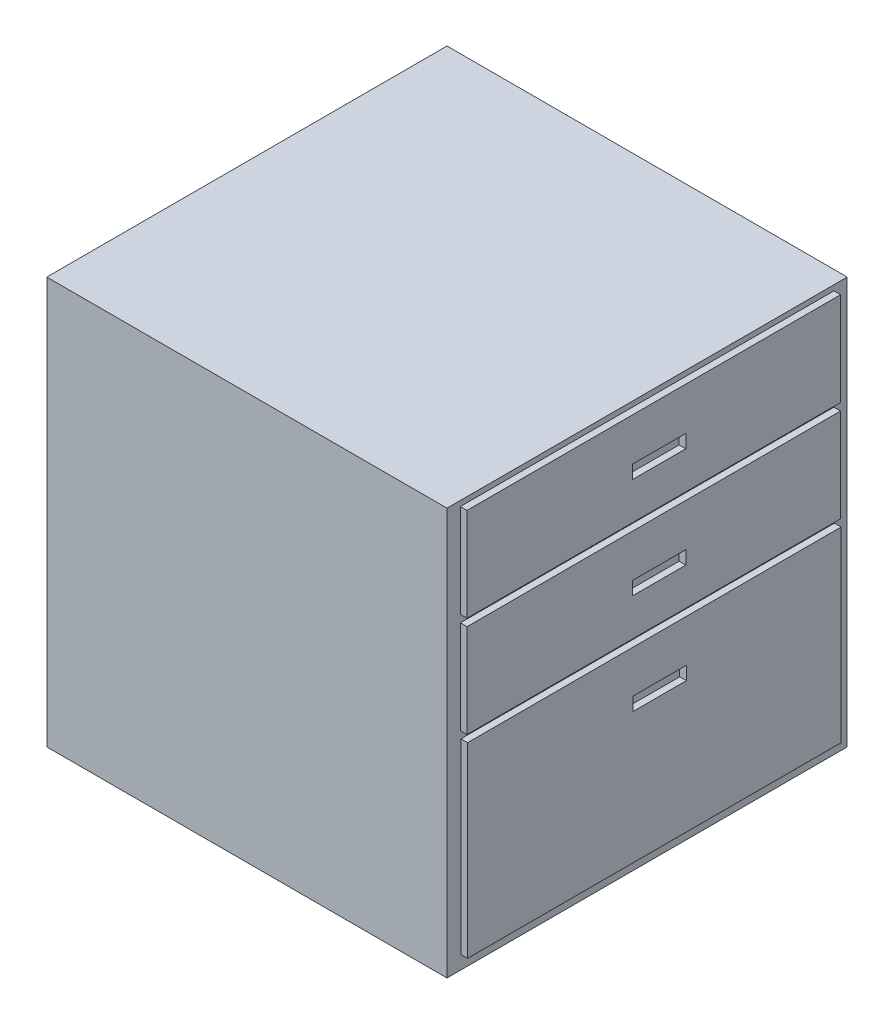
SolidWorks part; units mm, degrees
ref_plane "Front Plane" through (0, 0, 0) normal (0, 0, 1) x (1, 0, 0)
ref_plane "Top Plane" through (0, 0, 0) normal (0, 1, 0) x (1, 0, 0)
ref_plane "Right Plane" through (0, 0, 0) normal (1, 0, 0) x (0, 0, -1)
sketch "Sketch1" plane through (0, 0, 0) normal (0, 0, 1) x (1, 0, 0)
  line L1 (0, 0) -> (-600, 0)
  line L2 (0, 0) -> (0, -610)
  line L3 (0, -610) -> (-600, -610)
  line L4 (-600, 0) -> (-600, -610)
  dimension "D1" = 610
  dimension "D2" = 600
extrude "Boss-Extrude1" add sketch "Sketch1" along normal blind 600
sketch "Sketch2" plane through (0, 0, 0) normal (1, 0, 0) x (0, 0, -1)
  line L0 (0, -610) -> (0, 0) construction
  line L1 (-580, -7.9138) -> (-20, -7.9138)
  line L2 (-580, -7.9138) -> (-580, -147.9138)
  line L3 (-580, -147.9138) -> (-20, -147.9138)
  line L4 (-20, -7.9138) -> (-20, -147.9138)
  line L5 (-580, -158.9138) -> (-20, -158.9138)
  line L6 (-580, -158.9138) -> (-580, -298.9138)
  line L7 (-580, -298.9138) -> (-20, -298.9138)
  line L8 (-20, -158.9138) -> (-20, -298.9138)
  line L9 (-332, -222.9138) -> (-252, -222.9138)
  line L10 (-332, -222.9138) -> (-332, -242.9138)
  line L11 (-332, -242.9138) -> (-252, -242.9138)
  line L12 (-252, -222.9138) -> (-252, -242.9138)
  line L13 (-332, -71.9138) -> (-252, -71.9138)
  line L14 (-332, -71.9138) -> (-332, -91.9138)
  line L15 (-332, -91.9138) -> (-252, -91.9138)
  line L16 (-252, -71.9138) -> (-252, -91.9138)
  line L17 (-600, -610) -> (-600, 0) construction
  line L18 (-579.1676, -309.9138) -> (-19.1676, -309.9138)
  line L19 (-579.1676, -309.9138) -> (-579.1676, -589.9138)
  line L20 (-579.1676, -589.9138) -> (-19.1676, -589.9138)
  line L21 (-19.1676, -309.9138) -> (-19.1676, -589.9138)
  line L22 (-331.1676, -373.4001) -> (-251.1676, -373.4001)
  line L23 (-331.1676, -373.4001) -> (-331.1676, -393.4001)
  line L24 (-331.1676, -393.4001) -> (-251.1676, -393.4001)
  line L25 (-251.1676, -373.4001) -> (-251.1676, -393.4001)
  dimension "D1" = 140
  dimension "D2" = 56
  dimension "D3" = 20
  dimension "D4" = 80
  dimension "D5" = 2
  dimension "D6" = 20
  dimension "D7" = 20
  dimension "D8" = 280
  dimension "D9" = 11
  dimension "D10" = 11
extrude "Boss-Extrude2" add sketch "Sketch2" along normal blind 10
